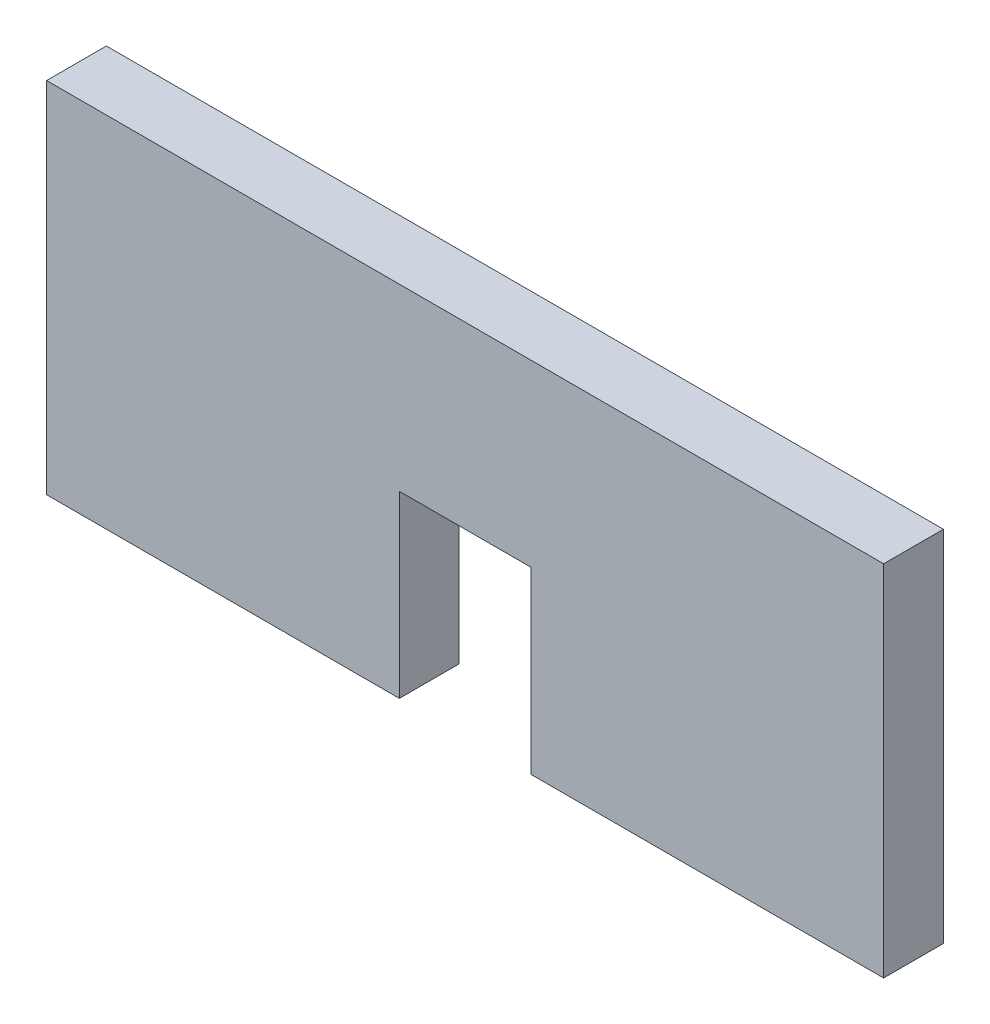
SolidWorks part; units mm, degrees
material "Plain Carbon Steel"
ref_plane "Front Plane" through (0, 0, 0) normal (0, 0, 1) x (1, 0, 0)
ref_plane "Top Plane" through (0, 0, 0) normal (0, 1, 0) x (1, 0, 0)
ref_plane "Right Plane" through (0, 0, 0) normal (1, 0, 0) x (0, 0, -1)
sketch "Sketch1" plane through (0, 0, 0) normal (0, 0, 1) x (1, 0, 0)
  line L0 (-295, 0) -> (0, 0)
  line L1 (-700, 300) -> (0, 300)
  line L2 (-700, 300) -> (-700, 0)
  line L3 (-700, 0) -> (-405, 0)
  line L4 (0, 300) -> (0, 0)
  line L5 (-405, 150) -> (-295, 150)
  line L6 (-405, 150) -> (-405, 0)
  line L8 (-295, 150) -> (-295, 0)
  dimension "D1" = 700
  dimension "D2" = 300
  dimension "D3" = 150
  dimension "D4" = 110
  dimension "D5" = 295
extrude "Boss-Extrude1" add sketch "Sketch1" along normal blind 50
